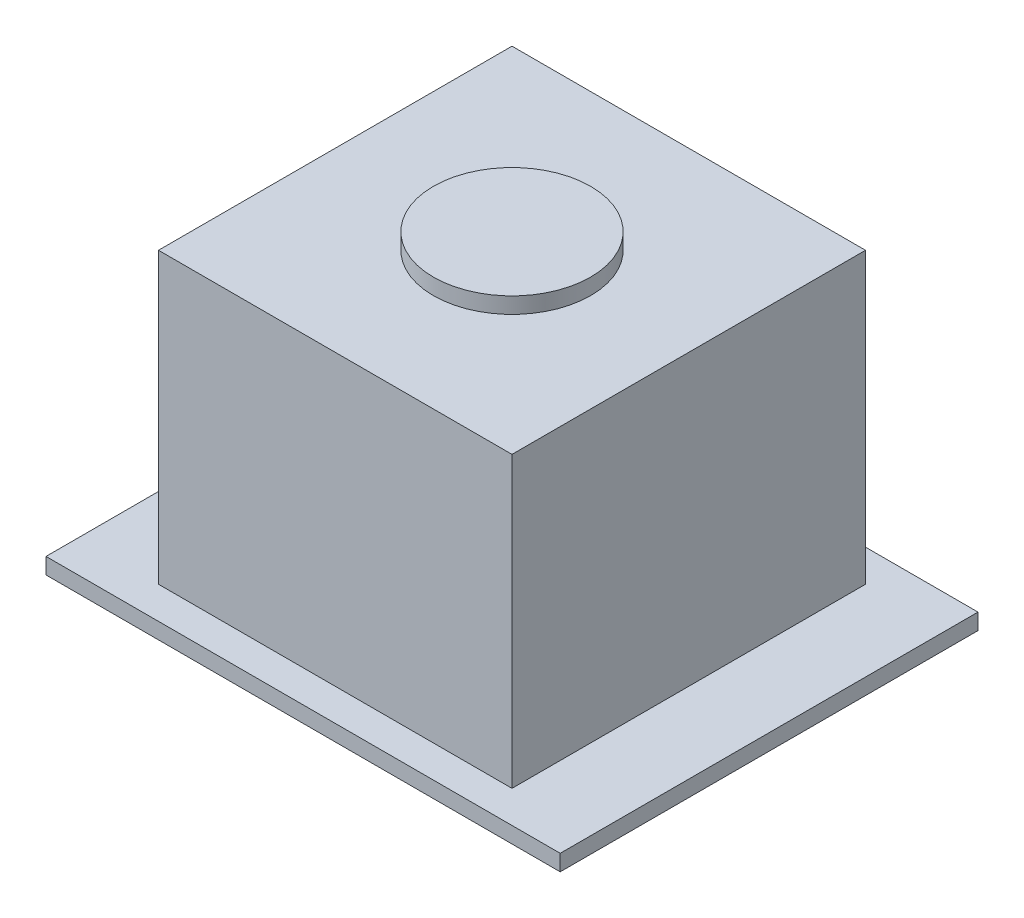
SolidWorks part; units mm, degrees
ref_plane "Front Plane" through (0, 0, 0) normal (0, 0, 1) x (1, 0, 0)
ref_plane "Top Plane" through (0, 0, 0) normal (0, 1, 0) x (1, 0, 0)
ref_plane "Right Plane" through (0, 0, 0) normal (1, 0, 0) x (0, 0, -1)
sketch "Sketch1" plane through (0, 0, 0) normal (0, 1, 0) x (1, 0, 0)
  line L1 (132.9765, -96.626) -> (143.9765, -96.626)
  line L2 (132.9765, -96.626) -> (132.9765, -107.626)
  line L3 (132.9765, -107.626) -> (143.9765, -107.626)
  line L4 (143.9765, -96.626) -> (143.9765, -107.626)
  dimension "D1" = 11
  dimension "D2" = 11
extrude "Boss-Extrude1" add sketch "Sketch1" along normal blind 9
sketch "Sketch2" plane through (0, 0, 0) normal (0, -1, 0) x (1, 0, 0)
  line L0 (132.9765, 96.626) -> (132.9765, 107.626) construction
  line L1 (130.4765, 108.626) -> (146.4765, 108.626)
  line L2 (130.4765, 108.626) -> (130.4765, 95.626)
  line L3 (130.4765, 95.626) -> (146.4765, 95.626)
  line L4 (146.4765, 108.626) -> (146.4765, 95.626)
  line L5 (132.9765, 107.626) -> (143.9765, 107.626) construction
  point P6 (132.9765, 102.126)
  point P7 (130.4765, 102.126)
  point P10 (138.4765, 107.626)
  point P11 (138.4765, 108.626)
  dimension "D1" = 13
  dimension "D2" = 16
extrude "Boss-Extrude2" add sketch "Sketch2" along normal blind 0.5
sketch "Sketch3" plane through (0, 9, 0) normal (0, 1, 0) x (1, 0, 0)
  line L0 (143.9765, -107.626) -> (143.9765, -96.626) construction
  circle A0 centre (138.4765, -102.126) radius 2.4466
  point P4 (143.9765, -102.126)
extrude "Boss-Extrude3" add sketch "Sketch3" along normal blind 0.5
